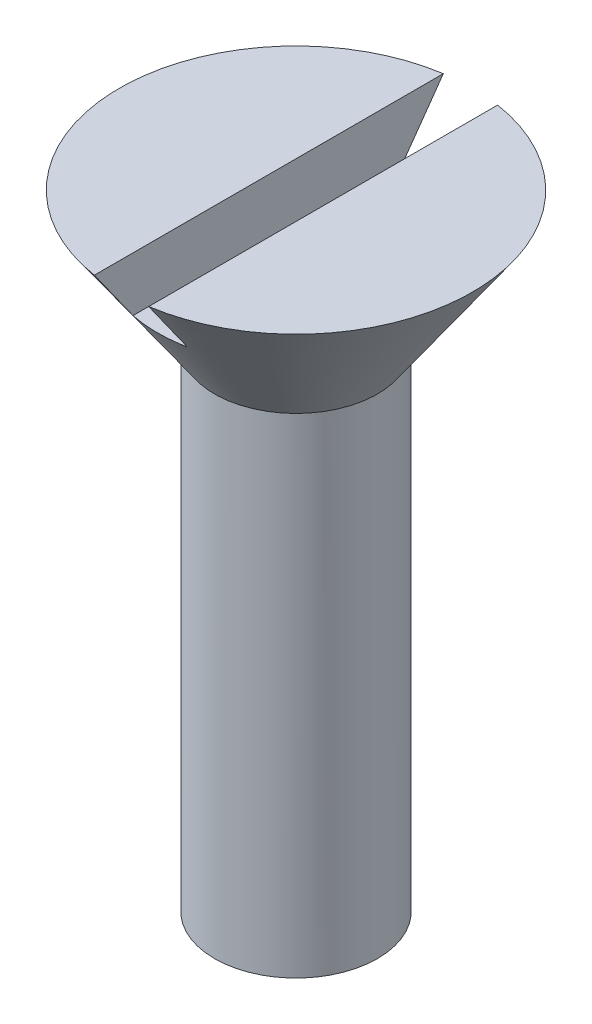
SolidWorks part; units mm, degrees
ref_plane "Front Plane" through (0, 0, 0) normal (0, 0, 1) x (1, 0, 0)
ref_plane "Top Plane" through (0, 0, 0) normal (0, 1, 0) x (1, 0, 0)
ref_plane "Right Plane" through (0, 0, 0) normal (1, 0, 0) x (0, 0, -1)
sketch "Sketch3" plane through (0, 0, 0) normal (0, 0, 1) x (1, 0, 0)
  line L0 (0, 0) -> (3, 1.7321)
  line L1 (3, 1.7321) -> (3, 19.7321)
  line L2 (3, 19.7321) -> (6.5, 24.7321)
  line L3 (6.5, 24.7321) -> (0, 24.7321)
  line L4 (0, -8.0008) -> (0, 57.1674) construction
  line L5 (0, 0) -> (0, 24.7321)
  point P8 (0, 0)
  dimension "D1" = 60
  dimension "D2" = 3
  dimension "D3" = 18
  dimension "D4" = 5
  dimension "D5" = 6.5
revolve "Revolve1" add sketch "Sketch3" angle 360 about L4
sketch "Sketch4" plane through (0, 0, 0) normal (0, 0, 1) x (1, 0, 0)
  line L0 (6.5, 24.7321) -> (-6.5, 24.7321) construction
  line L1 (-1, 25.7321) -> (1, 25.7321)
  line L2 (-1, 25.7321) -> (-1, 22.7321)
  line L3 (-1, 22.7321) -> (1, 22.7321)
  line L4 (1, 25.7321) -> (1, 22.7321)
  point P4 (0, 22.7321)
  dimension "D1" = 2
  dimension "D2" = 2
  dimension "D3" = 3
extrude "Cut-Extrude1" cut sketch "Sketch4" against normal through all both and the other way through all
